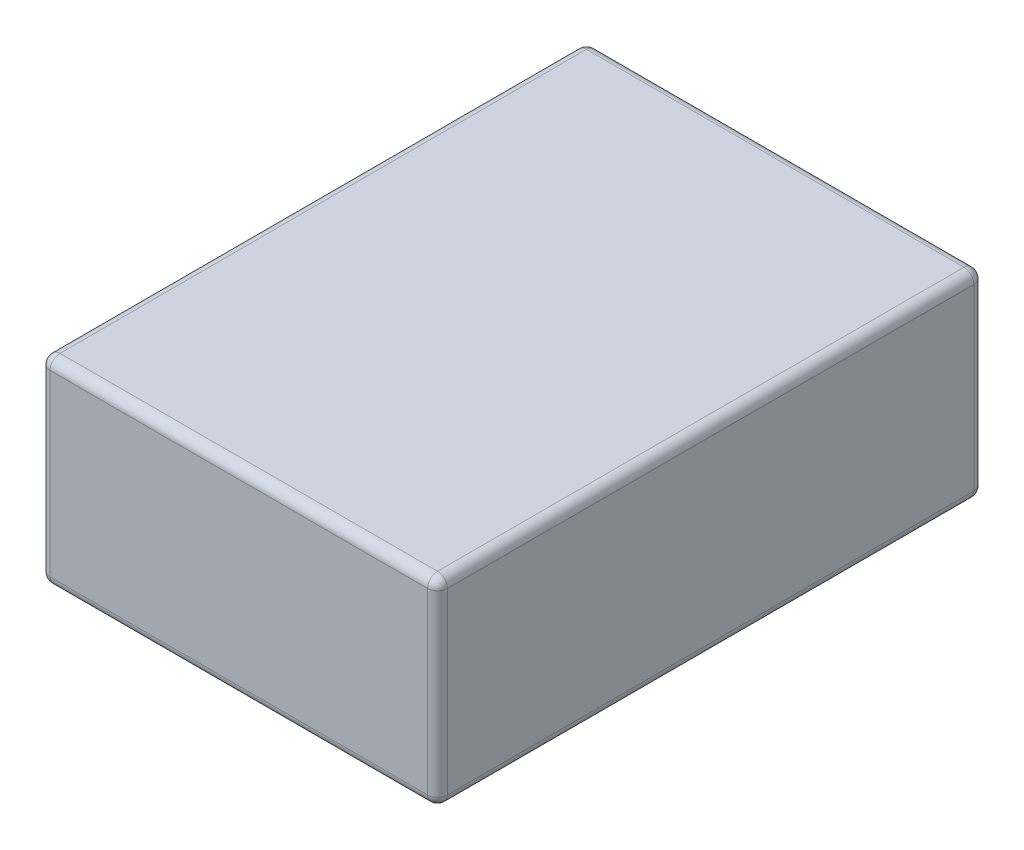
SolidWorks part; units mm, degrees
ref_plane "Front Plane" through (0, 0, 0) normal (0, 0, 1) x (1, 0, 0)
ref_plane "Top Plane" through (0, 0, 0) normal (0, 1, 0) x (1, 0, 0)
ref_plane "Right Plane" through (0, 0, 0) normal (1, 0, 0) x (0, 0, -1)
sketch "Sketch1" plane through (0, 0, 0) normal (0, 1, 0) x (1, 0, 0)
  line L1 (0, 0) -> (40, 0)
  line L2 (0, 0) -> (0, 55)
  line L3 (0, 55) -> (40, 55)
  line L4 (40, 0) -> (40, 55)
  dimension "D1" = 55
  dimension "D2" = 40
extrude "Boss-Extrude1" add sketch "Sketch1" along normal blind 20
fillet "Fillet1" radius 1 12 edges at (0, 10, 0) (40, 10, 0) (40, 10, -55) (0, 10, -55) (20, 20, -55) (40, 20, -27.5) (20, 20, 0) (0, 20, -27.5) (20, 0, 0) (40, 0, -27.5) (20, 0, -55) (0, 0, -27.5)
sketch "Sketch5" plane through (0, 20, 0) normal (0, 1, 0) x (1, 0, 0)
  line L0 (1, 54) -> (39, 1) construction
  text T0 "battery nikon EN-EL 15" font "Arial Narrow" height in points 16
extrude "Boss-Extrude2" add sketch "Sketch5" along direction (0, -1, 0) on the side against the normal offset from surface (2 mm away) 2
